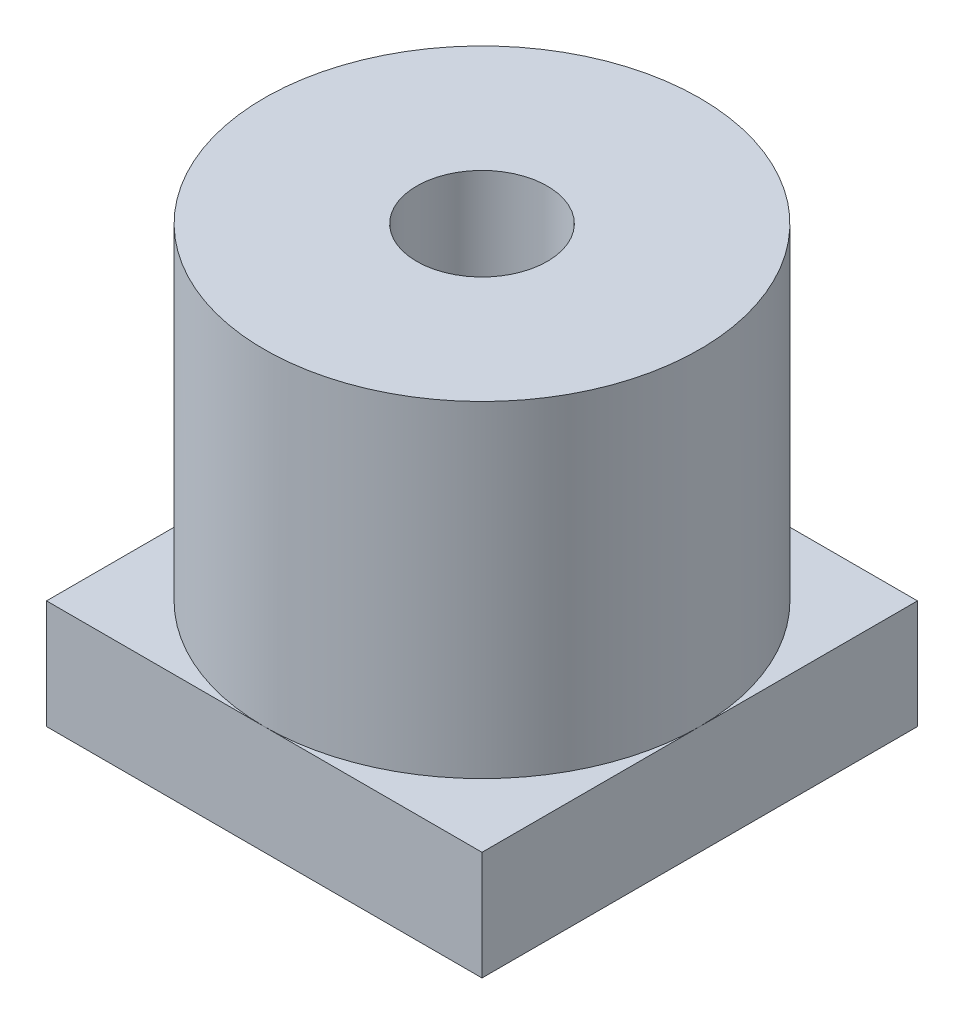
SolidWorks part; units mm, degrees
ref_plane "Front Plane" through (0, 0, 0) normal (0, 0, 1) x (1, 0, 0)
ref_plane "Top Plane" through (0, 0, 0) normal (0, 1, 0) x (1, 0, 0)
ref_plane "Right Plane" through (0, 0, 0) normal (1, 0, 0) x (0, 0, -1)
sketch "Sketch1" plane through (0, 0, 0) normal (0, 1, 0) x (1, 0, 0)
  line L1 (0, 0) -> (20, 0)
  line L2 (0, 0) -> (0, 20)
  line L3 (0, 20) -> (20, 20)
  line L4 (20, 0) -> (20, 20)
  dimension "D1" = 20
  dimension "D2" = 20
extrude "Boss-Extrude1" add sketch "Sketch1" along normal blind 20
sketch "Sketch2" plane through (0, 20, 0) normal (0, 1, 0) x (1, 0, 0)
  line L0 (20, 0) -> (20, 20) construction
  line L1 (0, 0) -> (20, 0) construction
  circle A0 centre (10, 10) radius 10
  point P4 (20, 10)
  dimension "D1" = 20
  dimension "D2" = 10
  dimension "D3" = 10
extrude "Cut-Extrude1" cut sketch "Sketch2" against normal blind 15 flip side to cut
sketch "Sketch3" plane through (0, 20, 0) normal (0, 1, 0) x (1, 0, 0)
  circle A0 centre (10, 10) radius 3
  dimension "D1" = 6
extrude "Cut-Extrude2" cut sketch "Sketch3" against normal through all
